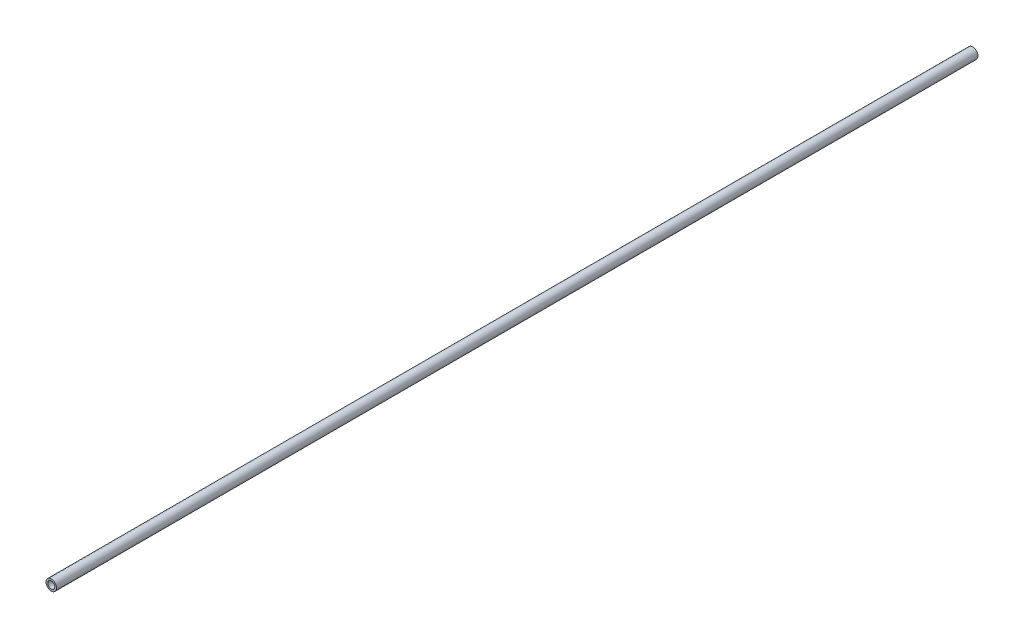
SolidWorks part; units mm, degrees
material "PVC Rigid"
ref_plane "Front Plane" through (0, 0, 0) normal (0, 0, 1) x (1, 0, 0)
ref_plane "Top Plane" through (0, 0, 0) normal (0, 1, 0) x (1, 0, 0)
ref_plane "Right Plane" through (0, 0, 0) normal (1, 0, 0) x (0, 0, -1)
sketch "Sketch1" plane through (0, 0, 0) normal (0, 0, 1) x (1, 0, 0)
  circle A0 centre (0, 0) radius 7.62
  circle A2 centre (0, 0) radius 5.08
  dimension "D1" = 15.24
  dimension "D2" = 10.16
extrude "Boss-Extrude1" add sketch "Sketch1" along normal blind 1333.5
